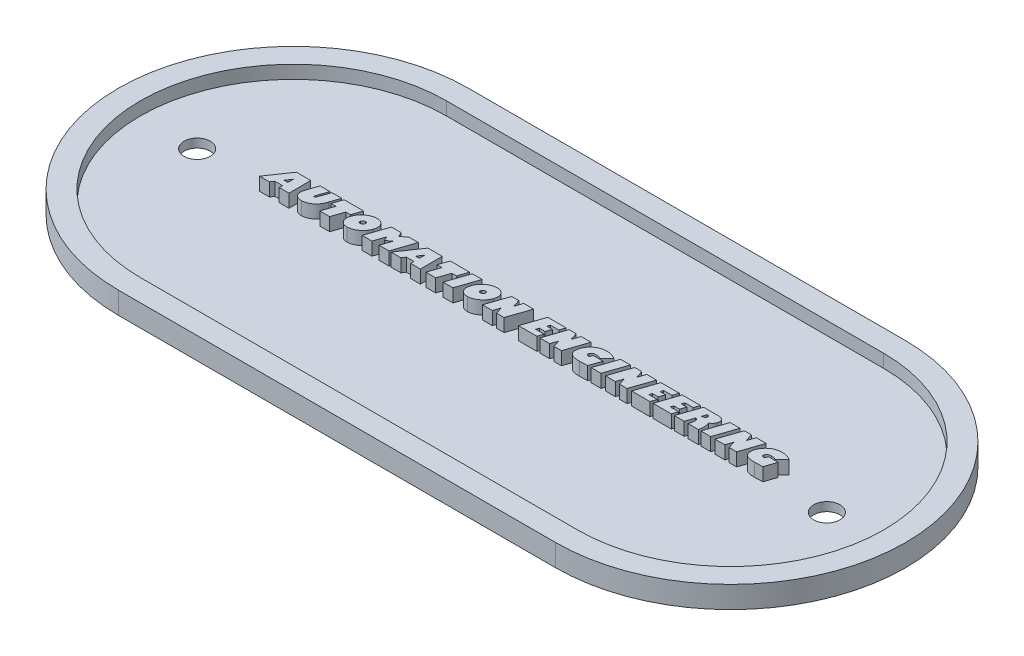
SolidWorks part; units mm, degrees
ref_plane "Front Plane" through (0, 0, 0) normal (0, 0, 1) x (1, 0, 0)
ref_plane "Top Plane" through (0, 0, 0) normal (0, 1, 0) x (1, 0, 0)
ref_plane "Right Plane" through (0, 0, 0) normal (1, 0, 0) x (0, 0, -1)
sketch "Sketch1" plane through (0, 0, 0) normal (0, 1, 0) x (1, 0, 0)
  line L0 (0, 0) -> (100, 0) construction
  line L1 (0, 40) -> (100, 40)
  line L2 (0, -40) -> (100, -40)
  arc A0 (0, 40) -> (0, -40) centre (0, 0) ccw
  arc A1 (100, -40) -> (100, 40) centre (100, 0) ccw
  point P3 (50, 0)
  dimension "D1" = 40
  dimension "D2" = 100
extrude "Boss-Extrude1" add sketch "Sketch1" along normal blind 5
sketch "Sketch2" plane through (0, 5, 0) normal (0, 1, 0) x (1, 0, 0)
  line L4 (100, 35) -> (0, 35)
  line L5 (0, -35) -> (100, -35)
  arc A4 (0, 35) -> (0, -35) centre (0, 0) ccw
  arc A5 (100, -35) -> (100, 35) centre (100, 0) ccw
extrude "Cut-Extrude1" cut sketch "Sketch2" against normal blind 3
sketch "Sketch3" plane through (0, 2, 0) normal (0, 1, 0) x (1, 0, 0)
  text T0 "AUTOMATION ENGINEERING" font "Gill Sans Ultra Bold" height 5
extrude "Boss-Extrude2" add sketch "Sketch3" along normal blind 3
sketch "Sketch4" plane through (0, 2, 0) normal (0, 1, 0) x (1, 0, 0)
  circle A0 centre (-22, 0) radius 3
  circle A1 centre (122, 0) radius 3
  arc A2 (0, 40) -> (0, -40) centre (0, 0) ccw construction
  arc A3 (100, -40) -> (100, 40) centre (100, 0) ccw construction
  dimension "D1" = 6
  dimension "D2" = 6
  dimension "D3" = 22
  dimension "D4" = 22
extrude "Cut-Extrude2" cut sketch "Sketch4" against normal through all
